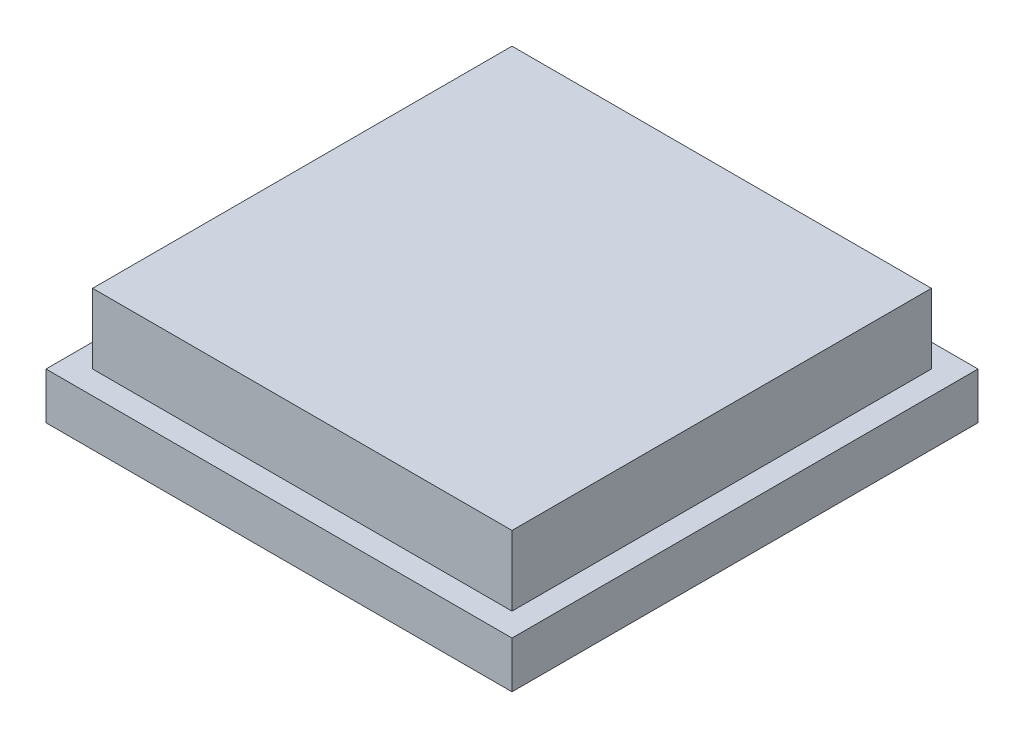
SolidWorks part; units mm, degrees
ref_plane "前视基准面" through (0, 0, 0) normal (0, 0, 1) x (1, 0, 0)
ref_plane "上视基准面" through (0, 0, 0) normal (0, 1, 0) x (1, 0, 0)
ref_plane "右视基准面" through (0, 0, 0) normal (1, 0, 0) x (0, 0, -1)
sketch "草图1" plane through (0, 0, 0) normal (0, 1, 0) x (1, 0, 0)
  line L1 (5, 5) -> (-5, 5)
  line L2 (5, 5) -> (5, -5)
  line L3 (5, -5) -> (-5, -5)
  line L4 (-5, 5) -> (-5, -5)
  line L5 (0, -5) -> (0, 5) construction
  line L6 (5, 0) -> (-5, 0) construction
  point P0 (0, 0)
  dimension "D1" = 10
  dimension "D2" = 10
extrude "凸台-拉伸1" add sketch "草图1" along normal blind 1
sketch "草图2" plane through (0, 0, 0) normal (0, 1, 0) x (1, 0, 0)
  line L1 (4.5, 4.5) -> (-4.5, 4.5)
  line L2 (4.5, 4.5) -> (4.5, -4.5)
  line L3 (4.5, -4.5) -> (-4.5, -4.5)
  line L4 (-4.5, 4.5) -> (-4.5, -4.5)
  line L5 (0, -4.5) -> (0, 4.5) construction
  line L6 (4.5, 0) -> (-4.5, 0) construction
  point P0 (0, 0)
  dimension "D1" = 9
  dimension "D2" = 9
extrude "凸台-拉伸2" add sketch "草图2" along normal blind 2.5
